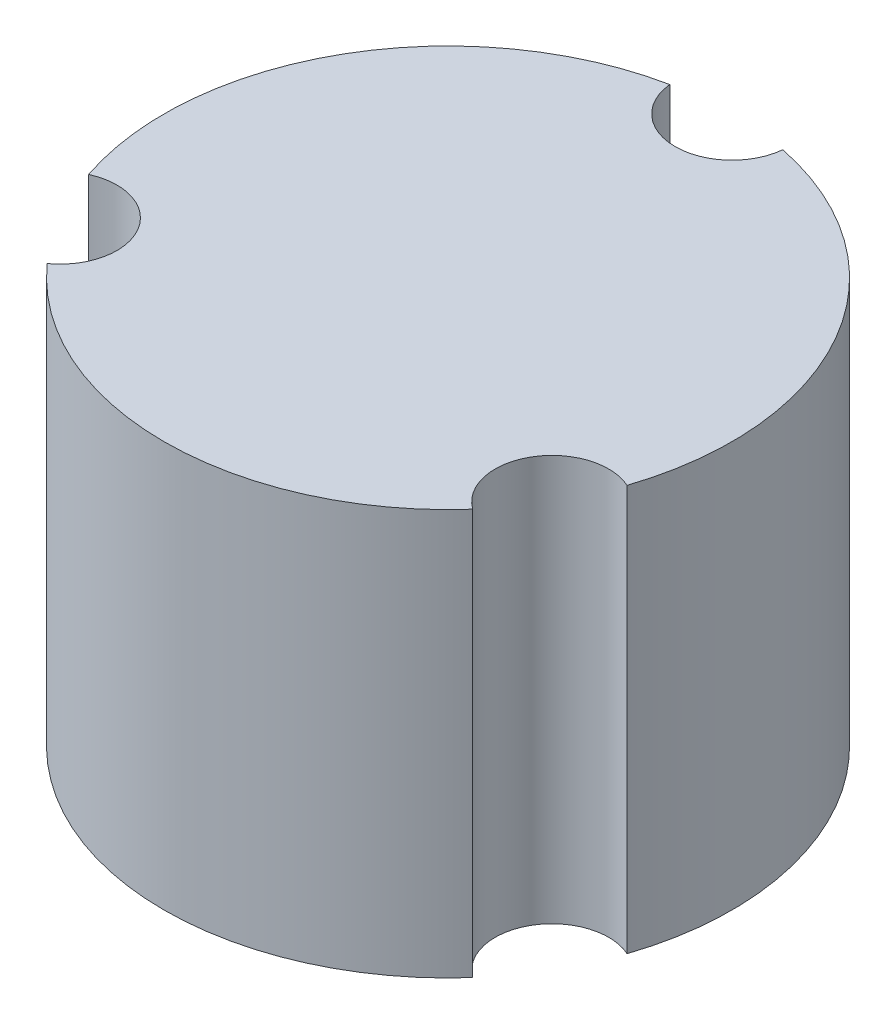
SolidWorks part; units mm, degrees
ref_plane "Alzado" through (0, 0, 0) normal (0, 0, 1) x (1, 0, 0)
ref_plane "Planta" through (0, 0, 0) normal (0, 1, 0) x (1, 0, 0)
ref_plane "Vista lateral" through (0, 0, 0) normal (1, 0, 0) x (0, 0, -1)
sketch "Croquis1" plane through (0, 0, 0) normal (0, 1, 0) x (1, 0, 0)
  circle A0 centre (0, 0) radius 22.225
  dimension "D1" = 44.45
extrude "Saliente-Extruir1" add sketch "Croquis1" along normal blind 31.75
sketch "Croquis2" plane through (0, 31.75, 0) normal (0, 1, 0) x (1, 0, 0)
  circle A0 centre (0, 22.225) radius 4.445
  circle A1 centre (0, 0) radius 22.225 construction
  circle A2 centre (19.2474, -11.1125) radius 4.445
  circle A3 centre (-19.2474, -11.1125) radius 4.445
  point P10 (0, 0)
  dimension "D1" = 8.89
  dimension "D2" = 3
extrude "Cortar-Extruir1" cut sketch "Croquis2" against normal through all
shell "Vaciado1" thickness 6.35
